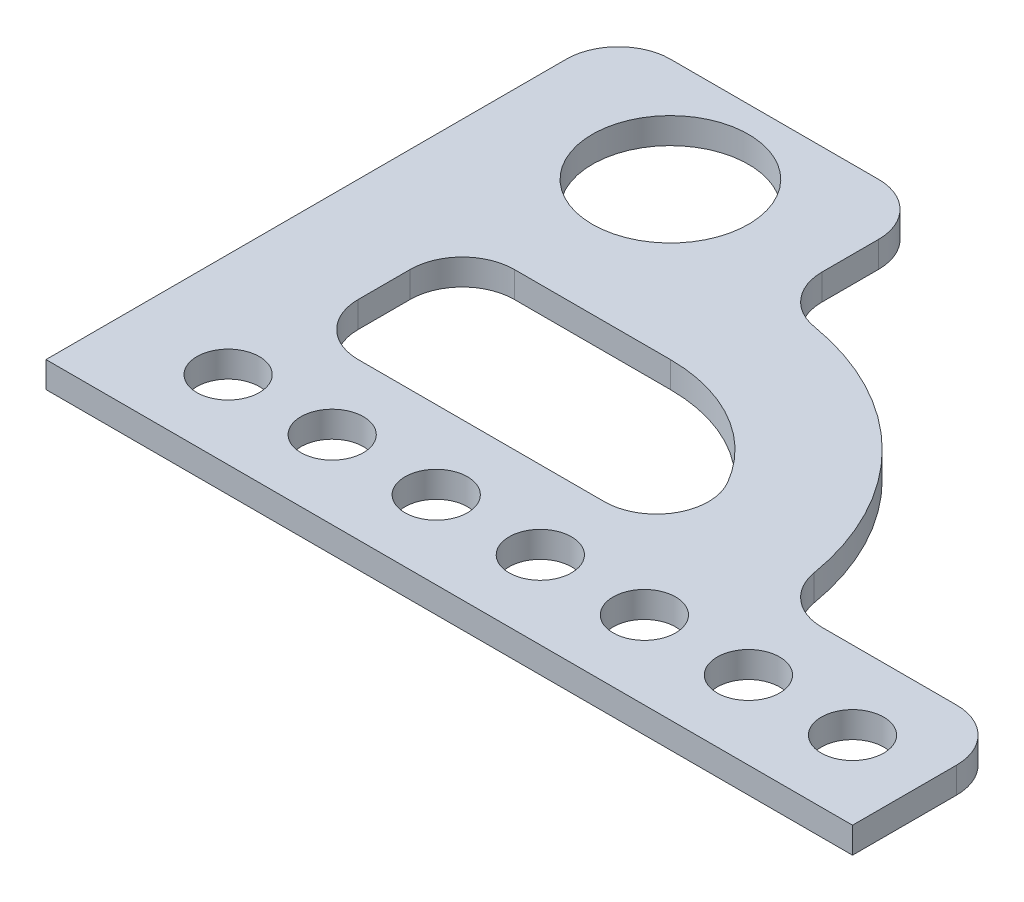
SolidWorks part; units mm, degrees
ref_plane "Front Plane" through (0, 0, 0) normal (0, 0, 1) x (1, 0, 0)
ref_plane "Top Plane" through (0, 0, 0) normal (0, 1, 0) x (1, 0, 0)
ref_plane "Right Plane" through (0, 0, 0) normal (1, 0, 0) x (0, 0, -1)
sketch "Sketch1" plane through (0, 0, 0) normal (0, 1, 0) x (1, 0, 0)
  line L0 (0, 0) -> (155, 0)
  line L1 (60, 60) -> (30, 60)
  line L2 (0, 0) -> (0, 100)
  line L3 (155, 0) -> (155, 20)
  line L4 (145, 30) -> (119.1608, 30)
  line L5 (10, 110) -> (50, 110)
  line L6 (60, 100) -> (60, 89.1608)
  line L18 (30, 30) -> (77.3205, 30)
  line L19 (20, 50) -> (20, 40)
  arc A0 (109.3007, 38.3333) -> (68.3333, 79.3007) centre (60, 30) ccw
  circle A1 centre (20, 15) radius 6
  circle A2 centre (40, 15) radius 6
  circle A3 centre (60, 15) radius 6
  circle A4 centre (80, 15) radius 6
  circle A5 centre (100, 15) radius 6
  circle A6 centre (120, 15) radius 6
  circle A7 centre (140, 15) radius 6
  circle A8 centre (30, 90) radius 15
  arc A9 (10, 110) -> (0, 100) centre (10, 100) ccw
  arc A10 (60, 100) -> (50, 110) centre (50, 100) ccw
  arc A11 (155, 20) -> (145, 30) centre (145, 20) ccw
  arc A12 (68.3333, 79.3007) -> (60, 89.1608) centre (70, 89.1608) cw
  arc A18 (119.1608, 30) -> (109.3007, 38.3333) centre (119.1608, 40) cw
  arc A24 (30, 60) -> (20, 50) centre (30, 50) ccw
  arc A25 (30, 30) -> (20, 40) centre (30, 40) cw
  arc A26 (85.9808, 45) -> (60, 60) centre (60, 30) ccw
  arc A27 (89.5804, 35) -> (65, 59.5804) centre (60, 30) ccw construction
  arc A28 (77.3205, 30) -> (85.9808, 45) centre (77.3205, 40) ccw
  point P27 (0, 110)
  point P30 (60, 110)
  point P33 (155, 30)
  point P36 (60, 80)
  point P39 (110, 30)
  point P50 (94.2734, 30)
  point P51 (65, 59.583)
  point P54 (57.1882, 60)
  point P55 (89.995, 29.4524)
  dimension "D6" = 50
  dimension "D8" = 7
  dimension "D10" = 12
  dimension "D11" = 15
  dimension "D12" = 30
  dimension "D15" = 20
  dimension "D16" = 10
  dimension "D17" = 10
  dimension "D18" = 10
  dimension "D19" = 10
  dimension "D20" = 10
  dimension "D21" = 30
  dimension "D23" = 10
  dimension "D22" = 10
  dimension "D24" = 20
  dimension "D25" = 30
  dimension "D26" = 10
  dimension "D1" = 110
  dimension "D2" = 155
  dimension "D3" = 30
  dimension "D4" = 60
  dimension "D5" = 45
  dimension "D7" = 30
  dimension "D9" = 120
  dimension "D13" = 30
  dimension "D14" = 20
  dimension "D27" = 40
extrude "Boss-Extrude1" add sketch "Sketch1" along normal blind 5
